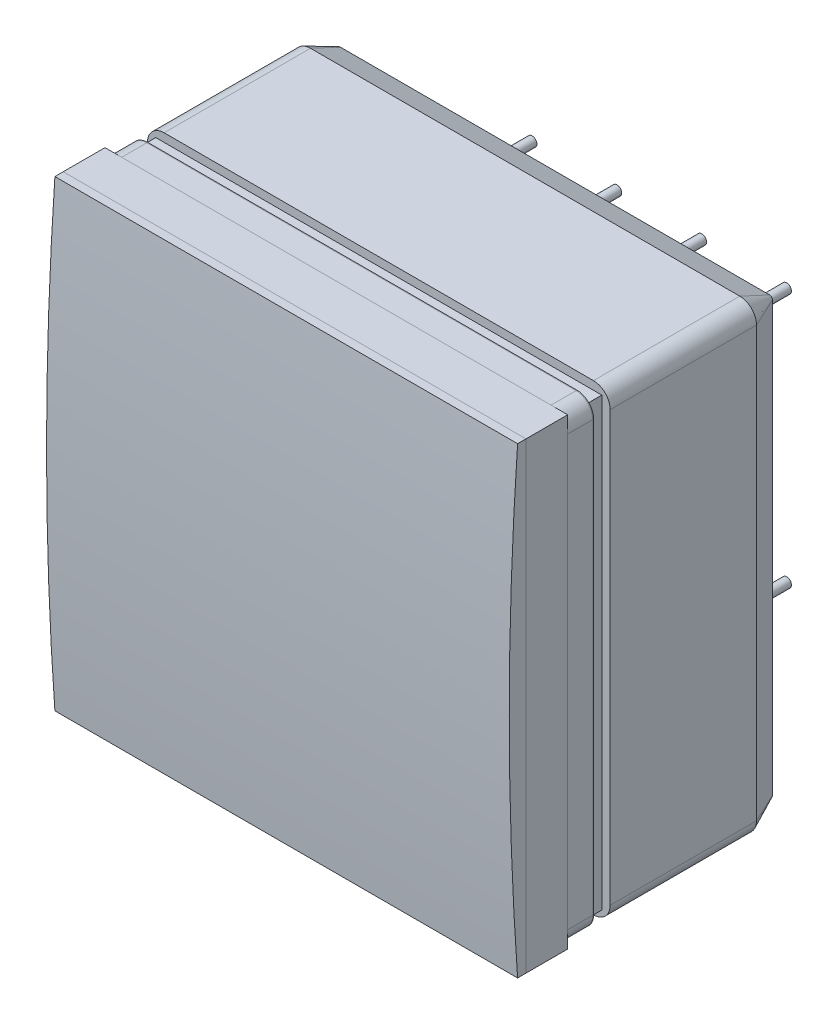
SolidWorks part; units mm, degrees
ref_plane "Front Plane" through (0, 0, 0) normal (0, 0, 1) x (1, 0, 0)
ref_plane "Top Plane" through (0, 0, 0) normal (0, 1, 0) x (1, 0, 0)
ref_plane "Right Plane" through (0, 0, 0) normal (1, 0, 0) x (0, 0, -1)
sketch "Sketch1" plane through (0, 0, 0) normal (0, 0, 1) x (1, 0, 0)
  line L1 (0, 0) -> (27.7, 0) construction
  line L2 (0, 0) -> (0, 27.7) construction
  line L3 (0, 27.7) -> (27.7, 27.7) construction
  line L4 (27.7, 0) -> (27.7, 27.7) construction
  line L5 (0.5, 0.5) -> (27.2, 0.5) construction
  line L6 (0.5, 0.5) -> (0.5, 27.2) construction
  line L7 (0.5, 27.2) -> (27.2, 27.2) construction
  line L8 (27.2, 0.5) -> (27.2, 27.2) construction
  line L9 (2.25, 2.25) -> (25.45, 2.25) construction
  line L10 (2.25, 2.25) -> (2.25, 25.45) construction
  line L11 (2.25, 25.45) -> (25.45, 25.45) construction
  line L12 (25.45, 2.25) -> (25.45, 25.45) construction
  line L13 (3.69, 3.69) -> (24.01, 3.69) construction
  line L14 (3.69, 3.69) -> (3.69, 24.01) construction
  line L15 (3.69, 24.01) -> (24.01, 24.01) construction
  line L16 (24.01, 3.69) -> (24.01, 24.01) construction
ref_plane "Plane1" through (0, 0, -2.54) normal (0, 0, 1) x (1, 0, 0)
sketch "Sketch2" plane through (0, 0, -2.54) normal (0, 0, 1) x (1, 0, 0)
  line L1 (1, 27.7) -> (26.7, 27.7)
  line L2 (0, 26.7) -> (0, 1)
  line L3 (1, 0) -> (26.7, 0)
  line L4 (27.7, 26.7) -> (27.7, 1)
  arc A0 (0, 1) -> (1, 0) centre (1, 1) ccw
  arc A1 (27.7, 1) -> (26.7, 0) centre (26.7, 1) cw
  arc A2 (27.7, 26.7) -> (26.7, 27.7) centre (26.7, 26.7) ccw
  arc A3 (1, 27.7) -> (0, 26.7) centre (1, 26.7) ccw
  dimension "D1" = 1
extrude "metal-case-at-HV" add sketch "Sketch2" against normal blind 8.76
sketch "Sketch3" plane through (0, 0, -2.54) normal (0, 0, 1) x (1, 0, 0)
  line L1 (1.3883, 26.1956) -> (26.126, 26.1956)
  line L2 (1.3883, 26.1956) -> (1.3883, 1.3651)
  line L3 (1.3883, 1.3651) -> (26.126, 1.3651)
  line L4 (26.126, 26.1956) -> (26.126, 1.3651)
extrude "photocathode" add sketch "Sketch3" along normal blind 0.1
sketch "Sketch5" plane through (0, 0, -2.54) normal (0, 0, 1) x (1, 0, 0)
  line L1 (0.5, 27.2) -> (27.2, 27.2)
  line L2 (0.5, 27.2) -> (0.5, 0.5)
  line L3 (0.5, 0.5) -> (27.2, 0.5)
  line L4 (27.2, 27.2) -> (27.2, 0.5)
  line L5 (2.25, 25.45) -> (25.45, 25.45)
  line L6 (2.25, 25.45) -> (2.25, 2.25)
  line L7 (2.25, 2.25) -> (25.45, 2.25)
  line L8 (25.45, 25.45) -> (25.45, 2.25)
extrude "Boss-Extrude3" add sketch "Sketch5" along normal blind 0.99
sketch "Sketch6" plane through (0, 0, -1.55) normal (0, 0, 1) x (1, 0, 0)
  line L1 (1, 27.7) -> (26.7, 27.7)
  line L2 (0, 26.7) -> (0, 1)
  line L3 (1, 0) -> (26.7, 0)
  line L4 (27.7, 26.7) -> (27.7, 1)
  line L5 (2.25, 25.45) -> (25.45, 25.45)
  line L6 (2.25, 25.45) -> (2.25, 2.25)
  line L7 (2.25, 2.25) -> (25.45, 2.25)
  line L8 (25.45, 25.45) -> (25.45, 2.25)
  arc A0 (0, 26.7) -> (1, 27.7) centre (1, 26.7) cw
  arc A1 (0, 1) -> (1, 0) centre (1, 1) ccw
  arc A2 (26.7, 0) -> (27.7, 1) centre (26.7, 1) ccw
  arc A3 (27.7, 26.7) -> (26.7, 27.7) centre (26.7, 26.7) ccw
  point P14 (0, 27.7)
  point P19 (27.7, 0)
  dimension "D1" = 1
  dimension "D2" = 1
extrude "mirrored-surface" add sketch "Sketch6" along normal blind 0.05
sketch "Sketch7" plane through (0, 0, -1.5) normal (0, 0, 1) x (1, 0, 0)
  line L1 (1, 27.7) -> (26.7, 27.7)
  line L2 (0, 26.7) -> (0, 1)
  line L3 (1, 0) -> (26.7, 0)
  line L4 (27.7, 26.7) -> (27.7, 1)
  arc A0 (0, 26.7) -> (1, 27.7) centre (1, 26.7) cw
  arc A1 (27.7, 26.7) -> (26.7, 27.7) centre (26.7, 26.7) ccw
  arc A2 (26.7, 0) -> (27.7, 1) centre (26.7, 1) ccw
  arc A3 (1, 0) -> (0, 1) centre (1, 1) cw
  point P9 (0, 27.7)
  point P13 (27.7, 0)
  dimension "D1" = 1
  dimension "D2" = 1
  dimension "D3" = 1
  dimension "D4" = 1
extrude "front-glass" add sketch "Sketch7" along normal blind 1.5 separate body
sketch "Sketch8" plane through (0, 0, -11.3) normal (0, 0, -1) x (-1, 0, 0)
  circle A0 centre (-24.01, 3.69) radius 0.285
  circle A1 centre (-21.47, 3.69) radius 0.285
  circle A2 centre (-18.93, 3.69) radius 0.285
  circle A3 centre (-16.39, 3.69) radius 0.285
  circle A4 centre (-13.85, 3.69) radius 0.285
  circle A5 centre (-11.31, 3.69) radius 0.285
  circle A6 centre (-8.77, 3.69) radius 0.285
  circle A7 centre (-6.23, 3.69) radius 0.285
  circle A8 centre (-3.69, 3.69) radius 0.285
  circle A9 centre (-24.01, 6.23) radius 0.285
  circle A10 centre (-21.47, 6.23) radius 0.285
  circle A11 centre (-18.93, 6.23) radius 0.285
  circle A12 centre (-16.39, 6.23) radius 0.285
  circle A13 centre (-13.85, 6.23) radius 0.285
  circle A14 centre (-11.31, 6.23) radius 0.285
  circle A15 centre (-8.77, 6.23) radius 0.285
  circle A16 centre (-6.23, 6.23) radius 0.285
  circle A17 centre (-3.69, 6.23) radius 0.285
  circle A18 centre (-24.01, 8.77) radius 0.285
  circle A19 centre (-21.47, 8.77) radius 0.285
  circle A20 centre (-18.93, 8.77) radius 0.285
  circle A21 centre (-16.39, 8.77) radius 0.285
  circle A22 centre (-13.85, 8.77) radius 0.285
  circle A23 centre (-11.31, 8.77) radius 0.285
  circle A24 centre (-8.77, 8.77) radius 0.285
  circle A25 centre (-6.23, 8.77) radius 0.285
  circle A26 centre (-3.69, 8.77) radius 0.285
  circle A27 centre (-24.01, 11.31) radius 0.285
  circle A28 centre (-21.47, 11.31) radius 0.285
  circle A29 centre (-18.93, 11.31) radius 0.285
  circle A30 centre (-16.39, 11.31) radius 0.285
  circle A31 centre (-13.85, 11.31) radius 0.285
  circle A32 centre (-11.31, 11.31) radius 0.285
  circle A33 centre (-8.77, 11.31) radius 0.285
  circle A34 centre (-6.23, 11.31) radius 0.285
  circle A35 centre (-3.69, 11.31) radius 0.285
  circle A36 centre (-24.01, 13.85) radius 0.285
  circle A37 centre (-21.47, 13.85) radius 0.285
  circle A38 centre (-18.93, 13.85) radius 0.285
  circle A39 centre (-16.39, 13.85) radius 0.285
  circle A40 centre (-13.85, 13.85) radius 0.285
  circle A41 centre (-11.31, 13.85) radius 0.285
  circle A42 centre (-8.77, 13.85) radius 0.285
  circle A43 centre (-6.23, 13.85) radius 0.285
  circle A44 centre (-3.69, 13.85) radius 0.285
  circle A45 centre (-24.01, 16.39) radius 0.285
  circle A46 centre (-21.47, 16.39) radius 0.285
  circle A47 centre (-18.93, 16.39) radius 0.285
  circle A48 centre (-16.39, 16.39) radius 0.285
  circle A49 centre (-13.85, 16.39) radius 0.285
  circle A50 centre (-11.31, 16.39) radius 0.285
  circle A51 centre (-8.77, 16.39) radius 0.285
  circle A52 centre (-6.23, 16.39) radius 0.285
  circle A53 centre (-3.69, 16.39) radius 0.285
  circle A54 centre (-24.01, 18.93) radius 0.285
  circle A55 centre (-21.47, 18.93) radius 0.285
  circle A56 centre (-18.93, 18.93) radius 0.285
  circle A57 centre (-16.39, 18.93) radius 0.285
  circle A58 centre (-13.85, 18.93) radius 0.285
  circle A59 centre (-11.31, 18.93) radius 0.285
  circle A60 centre (-8.77, 18.93) radius 0.285
  circle A61 centre (-6.23, 18.93) radius 0.285
  circle A62 centre (-3.69, 18.93) radius 0.285
  circle A63 centre (-24.01, 21.47) radius 0.285
  circle A64 centre (-21.47, 21.47) radius 0.285
  circle A65 centre (-18.93, 21.47) radius 0.285
  circle A66 centre (-16.39, 21.47) radius 0.285
  circle A67 centre (-13.85, 21.47) radius 0.285
  circle A68 centre (-11.31, 21.47) radius 0.285
  circle A69 centre (-8.77, 21.47) radius 0.285
  circle A70 centre (-6.23, 21.47) radius 0.285
  circle A71 centre (-3.69, 21.47) radius 0.285
  circle A72 centre (-24.01, 24.01) radius 0.285
  circle A73 centre (-21.47, 24.01) radius 0.285
  circle A74 centre (-18.93, 24.01) radius 0.285
  circle A75 centre (-16.39, 24.01) radius 0.285
  circle A76 centre (-13.85, 24.01) radius 0.285
  circle A77 centre (-11.31, 24.01) radius 0.285
  circle A78 centre (-8.77, 24.01) radius 0.285
  circle A79 centre (-6.23, 24.01) radius 0.285
  circle A80 centre (-3.69, 24.01) radius 0.285
extrude "pins" add sketch "Sketch8" along normal blind 5.5
sketch "Sketch9" plane through (0, 0, -16.8) normal (0, 0, -1) x (-1, 0, 0)
  line L0 (-22.1816, 24.8612) -> (-20.7784, 24.8612)
  line L1 (-22.1816, 24.8612) -> (-22.1816, 23.3649)
  line L2 (-22.1816, 23.3649) -> (-20.7784, 23.3649)
  line L3 (-20.7784, 24.8612) -> (-20.7784, 23.3649)
  line L4 (-17.3107, 24.8612) -> (-15.8078, 24.8612)
  line L5 (-17.3107, 24.8612) -> (-17.3107, 22.981)
  line L6 (-17.3107, 22.981) -> (-15.8078, 22.981)
  line L7 (-15.8078, 24.8612) -> (-15.8078, 22.981)
  line L8 (-11.8655, 24.8612) -> (-10.4335, 24.8612)
  line L9 (-11.8655, 24.8612) -> (-11.8655, 22.981)
  line L10 (-11.8655, 22.981) -> (-10.4335, 22.981)
  line L11 (-10.4335, 24.8612) -> (-10.4335, 22.981)
  line L12 (-7.2079, 24.8612) -> (-2.98, 24.8612)
  line L13 (-7.2079, 24.8612) -> (-7.2079, 23.3649)
  line L14 (-7.2079, 23.3649) -> (-2.98, 23.3649)
  line L15 (-2.98, 24.8612) -> (-2.98, 23.3649)
  line L16 (-24.8835, 22.2271) -> (-23.0472, 22.2271)
  line L17 (-24.8835, 22.2271) -> (-24.8835, 10.532)
  line L18 (-24.8835, 10.532) -> (-23.0472, 10.532)
  line L19 (-23.0472, 22.2271) -> (-23.0472, 10.532)
  line L20 (-24.8835, 7.577) -> (-23.0472, 7.577)
  line L21 (-24.8835, 7.577) -> (-24.8835, 2.706)
  line L22 (-24.8835, 2.706) -> (-23.0472, 2.706)
  line L23 (-23.0472, 7.577) -> (-23.0472, 2.706)
  line L24 (-19.7935, 22.4499) -> (-17.9649, 22.4499)
  line L25 (-19.7935, 22.4499) -> (-19.7935, 20.7304)
  line L26 (-19.7935, 20.7304) -> (-17.9649, 20.7304)
  line L27 (-17.9649, 22.4499) -> (-17.9649, 20.7304)
  line L28 (-14.5667, 22.4499) -> (-12.9507, 22.4499)
  line L29 (-14.5667, 22.4499) -> (-14.5667, 20.7304)
  line L30 (-14.5667, 20.7304) -> (-12.9507, 20.7304)
  line L31 (-12.9507, 22.4499) -> (-12.9507, 20.7304)
  line L32 (-9.3756, 22.4499) -> (-8.0103, 22.4499)
  line L33 (-9.3756, 22.4499) -> (-9.3756, 20.7304)
  line L34 (-9.3756, 20.7304) -> (-8.0103, 20.7304)
  line L35 (-8.0103, 22.4499) -> (-8.0103, 20.7304)
  line L36 (-4.5054, 22.2271) -> (-2.98, 22.2271)
  line L37 (-4.5054, 22.2271) -> (-4.5054, 20.7304)
  line L38 (-4.5054, 20.7304) -> (-2.98, 20.7304)
  line L39 (-2.98, 22.2271) -> (-2.98, 20.7304)
  line L40 (-22.4238, 19.8145) -> (-5.3688, 19.8145)
  line L41 (-22.4238, 19.8145) -> (-22.4238, 18.3702)
  line L42 (-22.4238, 18.3702) -> (-5.3688, 18.3702)
  line L43 (-5.3688, 19.8145) -> (-5.3688, 18.3702)
  line L44 (-22.4238, 14.7607) -> (-5.3688, 14.7607)
  line L45 (-22.4238, 14.7607) -> (-22.4238, 13.143)
  line L46 (-22.4238, 13.143) -> (-5.3688, 13.143)
  line L47 (-5.3688, 14.7607) -> (-5.3688, 13.143)
  line L48 (-22.4238, 9.6389) -> (-5.3688, 9.6389)
  line L49 (-22.4238, 9.6389) -> (-22.4238, 8.1251)
  line L50 (-22.4238, 8.1251) -> (-5.3688, 8.1251)
  line L51 (-5.3688, 9.6389) -> (-5.3688, 8.1251)
  line L52 (-4.5054, 17.5985) -> (-2.98, 17.5985)
  line L53 (-4.5054, 17.5985) -> (-4.5054, 2.706)
  line L54 (-4.5054, 2.706) -> (-2.98, 2.706)
  line L55 (-2.98, 17.5985) -> (-2.98, 2.706)
  line L56 (-19.7935, 17.3274) -> (-17.9649, 17.3274)
  line L57 (-19.7935, 17.3274) -> (-19.7935, 15.6815)
  line L58 (-19.7935, 15.6815) -> (-17.9649, 15.6815)
  line L59 (-17.9649, 17.3274) -> (-17.9649, 15.6815)
  line L60 (-14.5667, 17.3274) -> (-12.9507, 17.3274)
  line L61 (-14.5667, 17.3274) -> (-14.5667, 15.6815)
  line L62 (-14.5667, 15.6815) -> (-12.9507, 15.6815)
  line L63 (-12.9507, 17.3274) -> (-12.9507, 15.6815)
  line L64 (-9.3756, 17.3274) -> (-8.0103, 17.3274)
  line L65 (-9.3756, 17.3274) -> (-9.3756, 15.6815)
  line L66 (-9.3756, 15.6815) -> (-8.0103, 15.6815)
  line L67 (-8.0103, 17.3274) -> (-8.0103, 15.6815)
  line L68 (-9.3756, 12.3613) -> (-8.0103, 12.3613)
  line L69 (-9.3756, 12.3613) -> (-9.3756, 10.532)
  line L70 (-9.3756, 10.532) -> (-8.0103, 10.532)
  line L71 (-8.0103, 12.3613) -> (-8.0103, 10.532)
  line L72 (-9.3756, 7.021) -> (-8.2349, 7.021)
  line L73 (-9.3756, 7.021) -> (-9.3756, 5.5289)
  line L74 (-9.3756, 5.5289) -> (-8.2349, 5.5289)
  line L75 (-8.2349, 7.021) -> (-8.2349, 5.5289)
  line L76 (-14.9745, 7.021) -> (-13.2505, 7.021)
  line L77 (-14.9745, 7.021) -> (-14.9745, 5.5289)
  line L78 (-14.9745, 5.5289) -> (-13.2505, 5.5289)
  line L79 (-13.2505, 7.021) -> (-13.2505, 5.5289)
  line L80 (-14.5667, 12.1026) -> (-13.2505, 12.1026)
  line L81 (-14.5667, 12.1026) -> (-14.5667, 10.532)
  line L82 (-14.5667, 10.532) -> (-13.2505, 10.532)
  line L83 (-13.2505, 12.1026) -> (-13.2505, 10.532)
  line L84 (-19.7935, 12.3613) -> (-18.2001, 12.3613)
  line L85 (-19.7935, 12.3613) -> (-19.7935, 10.532)
  line L86 (-19.7935, 10.532) -> (-18.2001, 10.532)
  line L87 (-18.2001, 12.3613) -> (-18.2001, 10.532)
  line L88 (-19.7935, 7.021) -> (-17.9649, 7.021)
  line L89 (-19.7935, 7.021) -> (-19.7935, 5.5289)
  line L90 (-19.7935, 5.5289) -> (-17.9649, 5.5289)
  line L91 (-17.9649, 7.021) -> (-17.9649, 5.5289)
  line L92 (-22.4238, 4.9123) -> (-20.5348, 4.9123)
  line L93 (-22.4238, 4.9123) -> (-22.4238, 2.706)
  line L94 (-22.4238, 2.706) -> (-20.5348, 2.706)
  line L95 (-20.5348, 4.9123) -> (-20.5348, 2.706)
  line L96 (-17.3107, 4.4899) -> (-10.4335, 4.4899)
  line L97 (-17.3107, 4.4899) -> (-17.3107, 2.706)
  line L98 (-17.3107, 2.706) -> (-10.4335, 2.706)
  line L99 (-10.4335, 4.4899) -> (-10.4335, 2.706)
  line L100 (-7.5372, 4.4899) -> (-5.7773, 4.4899)
  line L101 (-7.5372, 4.4899) -> (-7.5372, 3.0088)
  line L102 (-7.5372, 3.0088) -> (-5.7773, 3.0088)
  line L103 (-5.7773, 4.4899) -> (-5.7773, 3.0088)
extrude "Cut-Extrude1" cut sketch "Sketch9" against normal blind 5.5
sketch "Sketch10" plane through (0, 0, -11.3) normal (0, 0, -1) x (-1, 0, 0)
  line L1 (-26.7, 27.7) -> (-1, 27.7)
  line L2 (-27.7, 26.7) -> (-27.7, 1)
  line L3 (-26.7, 0) -> (-1, 0)
  line L4 (0, 26.7) -> (0, 1)
  arc A0 (-26.7, 0) -> (-27.7, 1) centre (-26.7, 1) cw
  arc A1 (0, 26.7) -> (-1, 27.7) centre (-1, 26.7) ccw
  arc A2 (0, 1) -> (-1, 0) centre (-1, 1) cw
  arc A3 (-27.7, 26.7) -> (-26.7, 27.7) centre (-26.7, 26.7) cw
  point P11 (0, 0)
  dimension "D1" = 1
extrude "rubber" add sketch "Sketch10" along normal blind 1.79 draft 25 separate body
sketch "Sketch11" plane through (0, 0, -16.8) normal (0, 0, -1) x (-1, 0, 0)
  line L1 (-26.7, 27.7) -> (-1, 27.7) construction
  line L2 (-27.7, 26.7) -> (-27.7, 1) construction
  line L3 (-26.7, 0) -> (-1, 0) construction
  line L4 (0, 26.7) -> (0, 1) construction
  circle A0 centre (-24.01, 24.01) radius 0.285
  circle A1 centre (-18.93, 24.01) radius 0.285
  circle A2 centre (-13.85, 24.01) radius 0.285
  circle A3 centre (-8.77, 24.01) radius 0.285
  circle A4 centre (-6.23, 21.47) radius 0.285
  circle A5 centre (-11.31, 21.47) radius 0.285
  circle A6 centre (-16.39, 21.47) radius 0.285
  circle A7 centre (-21.47, 21.47) radius 0.285
  circle A8 centre (-21.47, 16.39) radius 0.285
  circle A9 centre (-16.39, 16.39) radius 0.285
  circle A10 centre (-11.31, 16.39) radius 0.285
  circle A11 centre (-6.23, 16.39) radius 0.285
  circle A12 centre (-3.69, 18.93) radius 0.285
  circle A13 centre (-21.47, 11.31) radius 0.285
  circle A14 centre (-16.39, 11.31) radius 0.285
  circle A15 centre (-11.31, 11.31) radius 0.285
  circle A16 centre (-6.23, 11.31) radius 0.285
  circle A17 centre (-24.01, 8.77) radius 0.285
  circle A18 centre (-21.47, 6.23) radius 0.285
  arc A19 (-26.7, 27.7) -> (-27.7, 26.7) centre (-26.7, 26.7) ccw construction
  circle A20 centre (-11.31, 6.23) radius 0.285
  circle A21 centre (-6.23, 6.23) radius 0.285
  circle A22 centre (-8.77, 3.69) radius 0.285
  circle A23 centre (-18.93, 3.69) radius 0.285
  circle A24 centre (-16.39, 6.23) radius 0.285
  arc A25 (-27.7, 1) -> (-26.7, 0) centre (-26.7, 1) ccw construction
  arc A26 (0, 1) -> (-1, 0) centre (-1, 1) cw construction
  arc A27 (0, 26.7) -> (-1, 27.7) centre (-1, 26.7) ccw construction
  dimension "D1" = 1
  dimension "D2" = 1
sketch "Sketch17" plane through (0, 0, 0) normal (0, 0, 1) x (1, 0, 0)
  line L1 (0, 27.7) -> (27.7, 27.7)
  line L2 (0, 27.7) -> (0, 0)
  line L3 (0, 0) -> (27.7, 0)
  line L4 (27.7, 27.7) -> (27.7, 0)
extrude "filter" add sketch "Sketch17" along normal blind 2.5 separate body
sketch "Sketch14" plane through (0, 0, 0) normal (1, 0, 0) x (0, 0, -1)
  line L0 (-2.5, 0) -> (-3.5, 0) construction
  line L3 (-3.5, 0) -> (-3.5, 27.7) construction
  line L4 (-3.5, 27.7) -> (-2.5, 27.7) construction
  line L5 (-2.5, 27.7) -> (-2.5, 0)
  line L6 (-3.5, 13.85) -> (-2.5, 13.85) construction
  line L7 (-3, 27.7) -> (-2.5, 27.7)
  line L8 (-3, 0) -> (-2.5, 0)
  arc A0 (-3.5, 13.85) -> (-3, 0) centre (188.5725, 13.85) ccw
  arc A2 (-3.5, 13.85) -> (-3, 27.7) centre (188.5725, 13.85) cw
extrude "cookie-cylindrical" add sketch "Sketch14" along normal up to surface (27.7 mm away) separate body up to face at (27.7, 13.85, -6.92)
